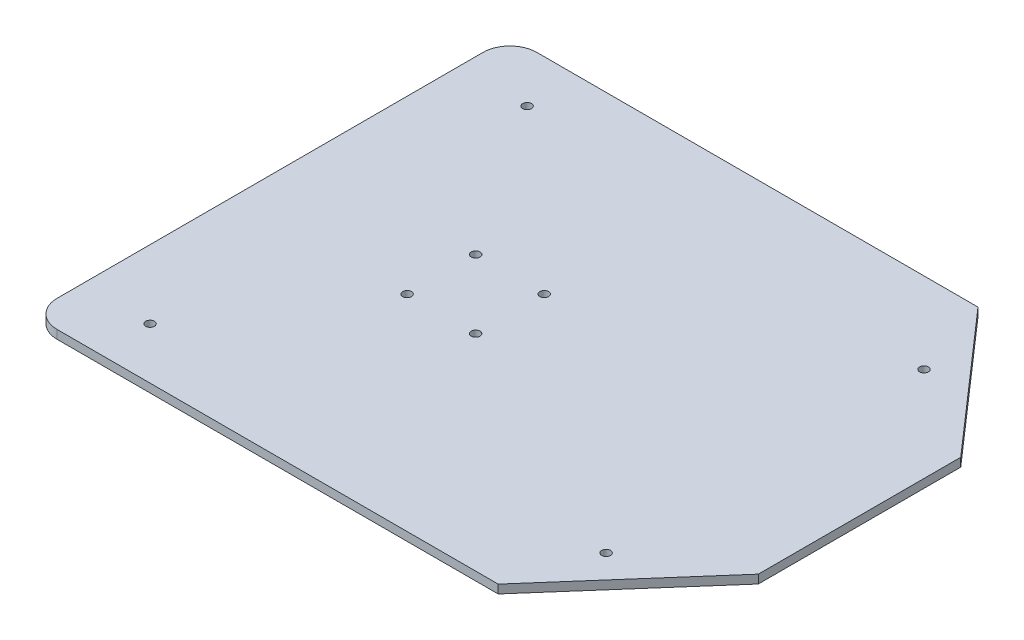
SolidWorks part; units mm, degrees
ref_plane "Front Plane" through (0, 0, 0) normal (0, 0, 1) x (1, 0, 0)
ref_plane "Top Plane" through (0, 0, 0) normal (0, 1, 0) x (1, 0, 0)
ref_plane "Right Plane" through (0, 0, 0) normal (1, 0, 0) x (0, 0, -1)
sketch "Sketch1" plane through (0, 0, 0) normal (0, 1, 0) x (1, 0, 0)
  line L0 (12.7, 12.7) -> (-12.7, 12.7) construction
  line L1 (-66.2, 88.9) -> (97.24, 88.9)
  line L2 (-76.2, 78.9) -> (-76.2, -78.9)
  line L3 (-66.2, -88.9) -> (97.24, -88.9)
  line L4 (142.24, 37.5) -> (142.24, -37.5)
  line L5 (-12.7, 12.7) -> (-12.7, -12.7) construction
  line L6 (97.24, 88.9) -> (142.24, 37.5)
  line L7 (142.24, -37.5) -> (97.24, -88.9)
  circle A1 centre (-12.7, 12.7) radius 1.6319
  circle A2 centre (12.7, 12.7) radius 1.632
  circle A3 centre (12.7, -12.7) radius 1.6319
  circle A4 centre (-12.7, -12.7) radius 1.6319
  arc A7 (-76.2, -78.9) -> (-66.2, -88.9) centre (-66.2, -78.9) ccw
  arc A8 (-66.2, 88.9) -> (-76.2, 78.9) centre (-66.2, 78.9) ccw
  circle A9 centre (-50.8, 69.85) radius 1.6319
  circle A10 centre (107.24, 58.9) radius 1.6319
  circle A11 centre (107.24, -58.9) radius 1.6319
  circle A12 centre (-50.8, -69.85) radius 1.6319
  circle A14 centre (0, 0) radius 152.4 construction
  point P0 (0, 12.7)
  point P1 (-12.7, 0)
  point P13 (0, 0)
  point P14 (142.24, 36.4586)
  point P15 (64.1927, 88.9)
  point P16 (103.0848, 88.9)
  dimension "D5" = 3.2639
  dimension "D16" = 10
  dimension "D1" = 25.4
  dimension "D2" = 25.4
  dimension "D6" = 63.5
  dimension "D7" = 129.54
  dimension "D3" = 76.2
  dimension "D4" = 76.2
  dimension "D10" = 19.05
  dimension "D11" = 19.05
  dimension "D12" = 25.4
  dimension "D13" = 30
  dimension "D14" = 30
  dimension "D15" = 35
  dimension "D8" = 75
  dimension "D9" = 45
extrude "Boss-Extrude1" add sketch "Sketch1" along normal blind 3.175
equation "\"D5@Sketch1\"=0.1285in"
equation "\"D4@Sketch1\"=\"D3@Sketch1\""
equation "\"D11@Sketch1\"=\"D10@Sketch1\""
equation "\"D14@Sketch1\"=\"D13@Sketch1\""
